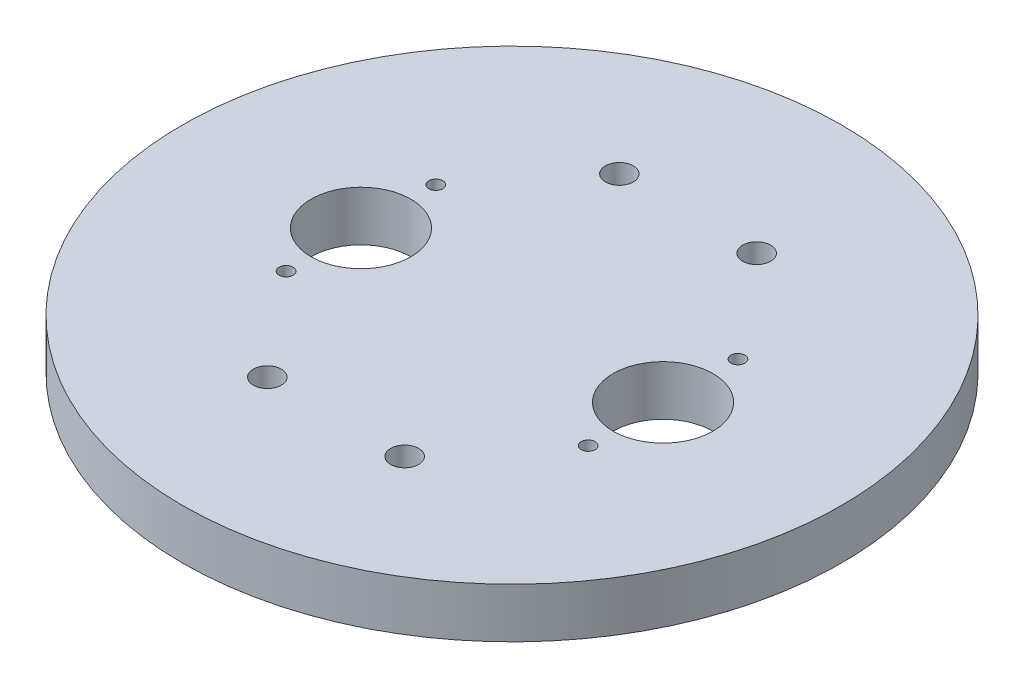
SolidWorks part; units mm, degrees
material "6061-T6 (SS)"
ref_plane "Front" through (0, 0, 0) normal (0, 0, 1) x (1, 0, 0)
ref_plane "Top" through (0, 0, 0) normal (0, 1, 0) x (1, 0, 0)
ref_plane "Right" through (0, 0, 0) normal (1, 0, 0) x (0, 0, -1)
sketch "Sketch1" plane through (0, 0, 0) normal (0, 1, 0) x (1, 0, 0)
  line L1 (0, 0) -> (127.635, 0)
  line L2 (0, 0) -> (0, 127.635)
  line L3 (0, 127.635) -> (127.635, 127.635)
  line L4 (127.635, 0) -> (127.635, 127.635)
  dimension "D1" = 127.635
  dimension "D2" = 127.635
extrude "Main Plate" add sketch "Sketch1" along normal blind 12.7
sketch "Sketch9" plane through (0, 12.7, 0) normal (0, 1, 0) x (1, 0, 0)
  circle A0 centre (63.8175, 63.8175) radius 83.82
  dimension "D1" = 167.64
extrude "Boss-Extrude1" add sketch "Sketch9" against normal up to surface (12.7 mm away) contours A0 up to face at (63.8175, 0, -63.8175)
sketch "Sketch10" plane through (0, 12.7, 0) normal (0, 1, 0) x (1, 0, 0)
  circle A0 centre (63.8175, 63.8175) radius 97.0396
  circle A1 centre (63.8175, 63.8175) radius 83.82
extrude "Cut-Extrude1" cut sketch "Sketch10" against normal blind 167.64 contours A0 | A1
sketch "Sketch11" plane through (0, 12.7, 0) normal (0, 1, 0) x (1, 0, 0)
  circle A0 centre (63.8175, 63.8175) radius 38.4175 construction
  circle A1 centre (63.8175, 63.8175) radius 42.8813 construction
  circle A2 centre (63.8175, 63.8175) radius 48.0528 construction
  dimension "D1" = 76.835
  dimension "D2" = 85.7626
  dimension "D3" = 96.1055
sketch "Sketch12" plane through (0, 12.7, 0) normal (0, 1, 0) x (1, 0, 0)
  line L0 (63.8175, 156.3529) -> (63.8175, -30.2474) construction
  line L1 (160.3603, 63.8175) -> (-31.9911, 63.8175) construction
sketch "Sketch2" plane through (0, 12.7, 0) normal (0, 1, 0) x (1, 0, 0)
  circle A0 centre (46.355, 108.585) radius 3.556
  circle A3 centre (63.8175, 63.8175) radius 48.0528 construction
  dimension "D1" = 7.112
extrude "U-Bolt Hole" cut sketch "Sketch2" against normal blind 12.7
pattern_linear "U-Bolt Pattern" count 2 spacing 34.925 along (1, 0, 0) count 2 spacing 89.535 along (0, 0, 1) of "U-Bolt Hole"
sketch "Sketch3" plane through (0, 12.7, 0) normal (0, 1, 0) x (1, 0, 0)
  circle A0 centre (25.4, 44.7675) radius 1.778
  circle A1 centre (63.8175, 63.8175) radius 42.8813 construction
  dimension "D1" = 3.556
extrude "Raptor Bolt Hole" cut sketch "Sketch3" against normal blind 12.7
pattern_linear "Raptor Bolt Pattern" count 2 spacing 38.1 along (0, 0, -1) count 2 spacing 76.835 along (1, 0, 0) of "Raptor Bolt Hole"
sketch "Sketch4" plane through (0, 12.7, 0) normal (0, 1, 0) x (1, 0, 0)
  circle A0 centre (25.4, 63.8175) radius 12.7
  circle A1 centre (63.8175, 63.8175) radius 38.4175 construction
  dimension "D1" = 25.4
extrude "Co2 Cylinder Hole" cut sketch "Sketch4" against normal blind 12.7
pattern_linear "Co2 Pattern" count 2 spacing 76.835 along (1, 0, 0) of "Co2 Cylinder Hole"
